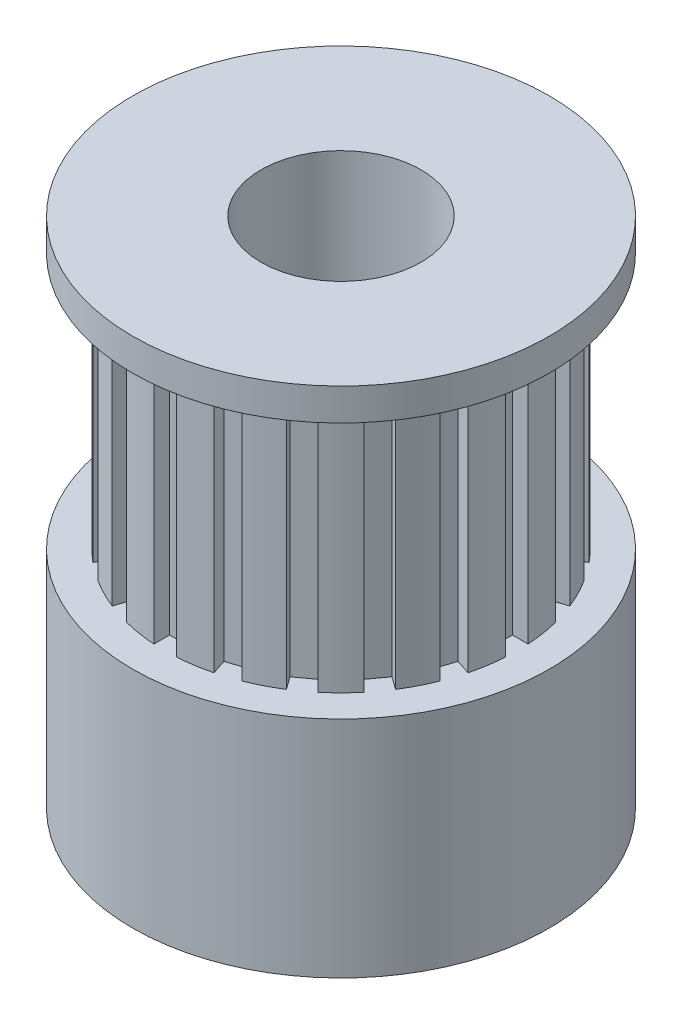
SolidWorks part; units mm, degrees
ref_plane "Front" through (0, 0, 0) normal (0, 0, 1) x (1, 0, 0)
ref_plane "Top" through (0, 0, 0) normal (0, 1, 0) x (1, 0, 0)
ref_plane "Right" through (0, 0, 0) normal (1, 0, 0) x (0, 0, -1)
sketch "Sketch1" plane through (0, 0, 0) normal (0, 1, 0) x (1, 0, 0)
  circle A0 centre (0, 0) radius 6.5
  circle A1 centre (0, 0) radius 2.5
  dimension "D1" = 13
  dimension "D2" = 5
extrude "Boss-Extrude1" add sketch "Sketch1" along normal blind 16
sketch "Sketch2" plane through (0, 0, 0) normal (0, 0, 1) x (1, 0, 0)
  line L0 (6.5, 0) -> (6.5, 16) construction
  line L1 (6.5, 15) -> (5.5, 15)
  line L2 (6.5, 15) -> (6.5, 7)
  line L3 (6.5, 7) -> (5.5, 7)
  line L4 (5.5, 15) -> (5.5, 7)
  line L5 (6.5, 16) -> (-6.5, 16) construction
  line L6 (0, 18.1948) -> (0, 1.9539) construction
  dimension "D1" = 1
  dimension "D2" = 8
  dimension "D3" = 1
revolve "Cut-Revolve1" cut sketch "Sketch2" angle 360 about L6
sketch "Sketch3" plane through (0, 0, 0) normal (0, 0, 1) x (1, 0, 0)
  circle A0 centre (0, 3.5) radius 1.5
extrude "Cut-Extrude1" cut sketch "Sketch3" against normal through all
pattern_circular "CirPattern1" count 2 over 90 about axis through (0, 16, 0) along (0, -1, 0) of "Cut-Extrude1"
ref_plane "Plane1" through (0, 0, 5.5) normal (0, 0, 1) x (1, 0, 0)
sketch "Sketch6" plane through (0, 0, 5.5) normal (0, 0, 1) x (1, 0, 0)
  line L1 (-0.35, 15) -> (0.35, 15)
  line L2 (-0.35, 15) -> (-0.35, 7)
  line L3 (-0.35, 7) -> (0.35, 7)
  line L4 (0.35, 15) -> (0.35, 7)
  line L5 (-0.35, 15) -> (0.35, 7) construction
  line L6 (-0.35, 7) -> (0.35, 15) construction
  point P0 (0, 11)
  dimension "D1" = 0.7
extrude "Cut-Extrude2" cut sketch "Sketch6" against normal blind 0.5
pattern_circular "CirPattern2" count 20 over 360 about axis through (0, 0, 0) along (0, 1, 0) of "Cut-Extrude2"
